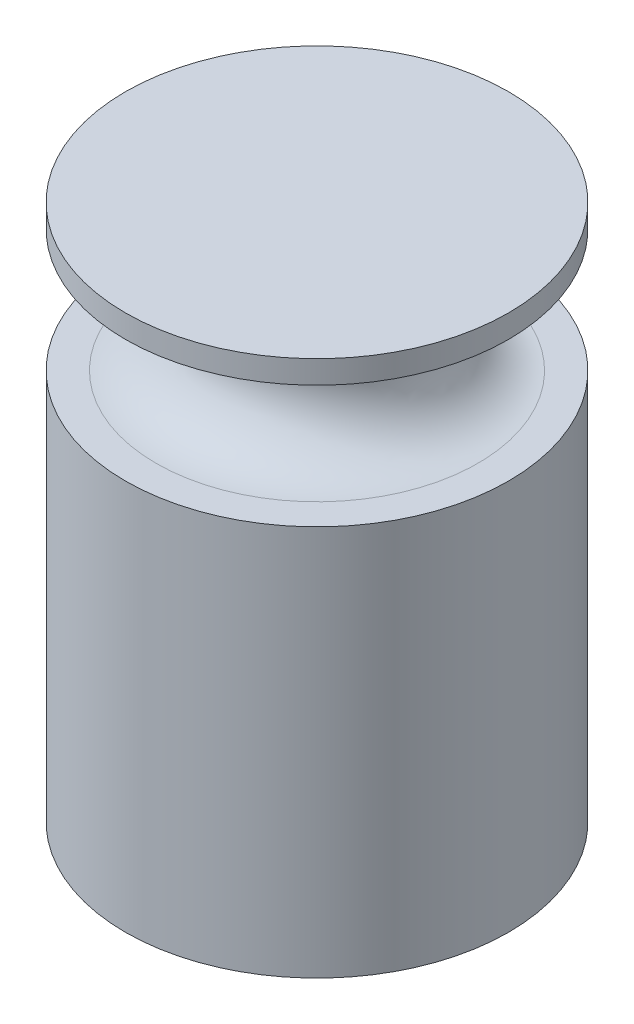
SolidWorks part; units mm, degrees
material "Brass"
ref_plane "Front" through (0, 0, 0) normal (0, 0, 1) x (1, 0, 0)
ref_plane "Top" through (0, 0, 0) normal (0, 1, 0) x (1, 0, 0)
ref_plane "Right" through (0, 0, 0) normal (1, 0, 0) x (0, 0, -1)
sketch "Sketch1" plane through (0, 0, 0) normal (0, 0, 1) x (1, 0, 0)
  line L0 (0, 0) -> (0, 70)
  line L1 (0, 0) -> (25, 0)
  line L2 (0, 70) -> (25, 70)
  line L3 (25, 0) -> (25, 51)
  line L4 (0, -50) -> (0, 50) construction
  line L6 (25, 67) -> (21, 67)
  line L7 (25, 51) -> (21, 51)
  line L9 (25, 67) -> (25, 70)
  arc A0 (21, 67) -> (21, 51) centre (21, 59) ccw
  point P10 (13, 59)
  dimension "D1" = 25
  dimension "D2" = 70
  dimension "D3" = 3
  dimension "D4" = 16
  dimension "D5" = 12
revolve "Revolve1" add sketch "Sketch1" angle 360 about L0
